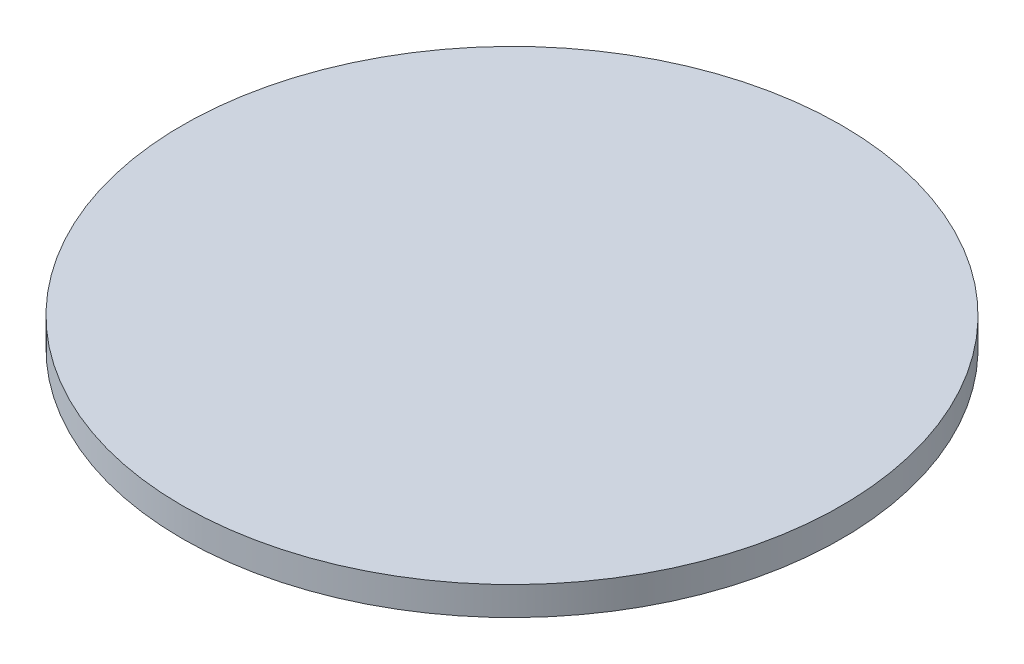
SolidWorks part; units mm, degrees
ref_plane "Front Plane" through (0, 0, 0) normal (0, 0, 1) x (1, 0, 0)
ref_plane "Top Plane" through (0, 0, 0) normal (0, 1, 0) x (1, 0, 0)
ref_plane "Right Plane" through (0, 0, 0) normal (1, 0, 0) x (0, 0, -1)
sketch "Sketch1" plane through (0, 0, 0) normal (0, 1, 0) x (1, 0, 0)
  circle A0 centre (0, 0) radius 36.576
  dimension "D1" = 73.152
extrude "Boss-Extrude1" add sketch "Sketch1" along normal mid plane 3.175
